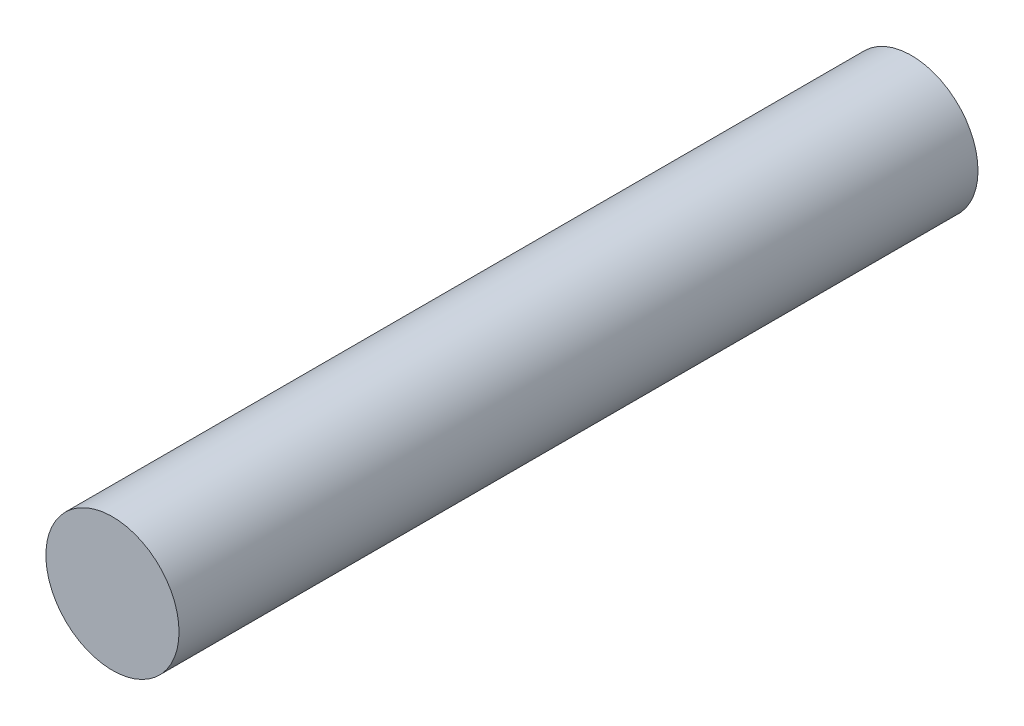
SolidWorks part; units mm, degrees
material "Plain Carbon Steel"
ref_plane "Front Plane" through (0, 0, 0) normal (0, 0, 1) x (1, 0, 0)
ref_plane "Top Plane" through (0, 0, 0) normal (0, 1, 0) x (1, 0, 0)
ref_plane "Right Plane" through (0, 0, 0) normal (1, 0, 0) x (0, 0, -1)
sketch "Sketch1" plane through (0, 0, 0) normal (0, 0, 1) x (1, 0, 0)
  circle A0 centre (0, 0) radius 4.7625
  dimension "D1" = 9.525
extrude "Boss-Extrude1" add sketch "Sketch1" against normal blind 57.15
